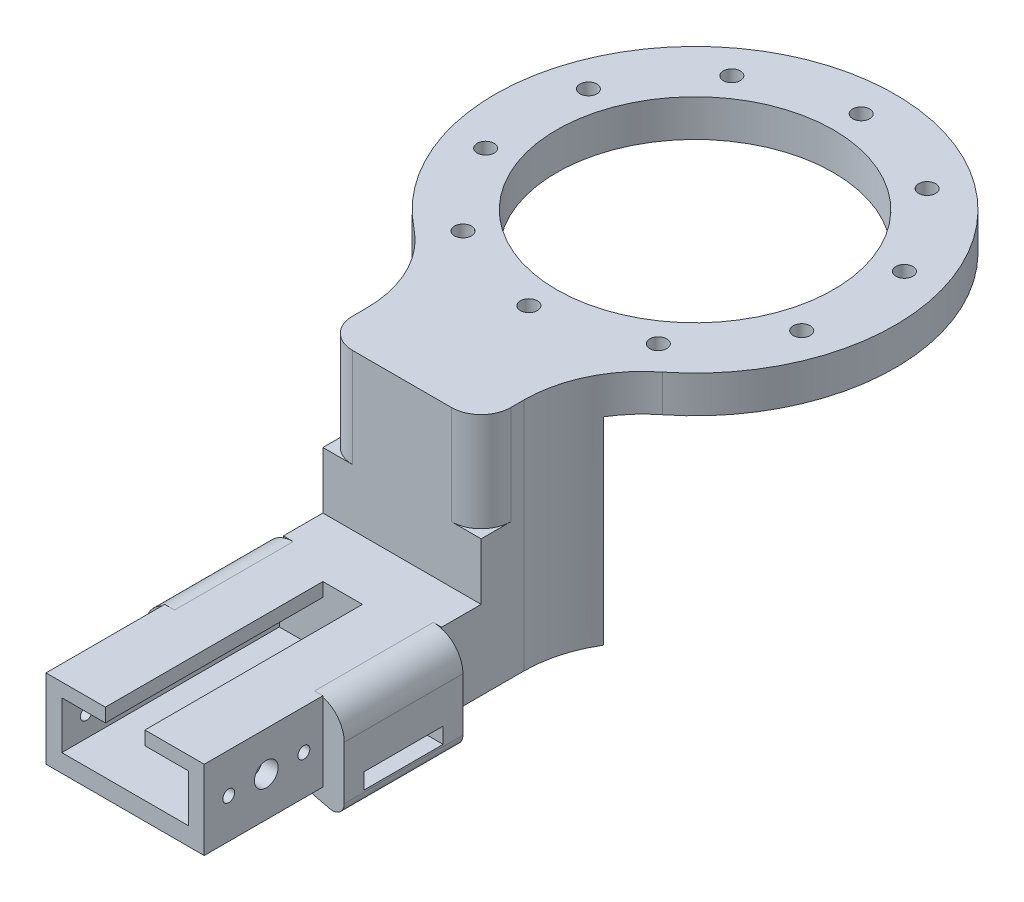
SolidWorks part; units mm, degrees
ref_plane "Front Plane" through (0, 0, 0) normal (0, 0, 1) x (1, 0, 0)
ref_plane "Top Plane" through (0, 0, 0) normal (0, 1, 0) x (1, 0, 0)
ref_plane "Right Plane" through (0, 0, 0) normal (1, 0, 0) x (0, 0, -1)
sketch "Sketch2" plane through (0, 0, 0) normal (0, 1, 0) x (1, 0, 0)
  line L0 (-20, -74.0815) -> (-20, -63.1931)
  line L1 (20, -74.0815) -> (20, -63.1931)
  line L8 (-20, -74.0815) -> (20, -74.0815)
  arc A0 (31.3853, -39.6667) -> (-31.3853, -39.6667) centre (0, 0) ccw
  circle A2 centre (0, 42) radius 2.1524
  circle A3 centre (24.687, 33.9787) radius 2.1524
  circle A4 centre (39.9444, 12.9787) radius 2.1524
  circle A5 centre (39.9444, -12.9787) radius 2.1524
  circle A6 centre (24.687, -33.9787) radius 2.1524
  circle A7 centre (0, -42) radius 2.1524
  circle A8 centre (-24.687, -33.9787) radius 2.1524
  circle A9 centre (-39.9444, -12.9787) radius 2.1524
  circle A10 centre (-39.9444, 12.9787) radius 2.1524
  circle A11 centre (-24.687, 33.9787) radius 2.1524
  circle A12 centre (0, 0) radius 35
  arc A14 (31.3853, -39.6667) -> (20, -63.1931) centre (50, -63.1931) ccw
  arc A15 (-20, -63.1931) -> (-31.3853, -39.6667) centre (-50, -63.1931) ccw
  point P26 (0, 0)
  dimension "D1" = 42
  dimension "D2" = 10
extrude "Boss-Extrude2" add sketch "Sketch2" along normal blind 9.35
sketch "Sketch4" plane through (0, 0, 0) normal (0, -1, 0) x (1, 0, 0)
  line L0 (-20, 74.0815) -> (20, 74.0815)
  line L5 (20, 74.0815) -> (20, 63.1931)
  line L6 (-20, 74.0815) -> (-20, 63.1931)
  arc A0 (20, 63.1931) -> (31.3853, 39.6667) centre (50, 63.1931) ccw construction
  arc A1 (-21.4172, 54.0815) -> (-20, 63.1931) centre (-50, 63.1931) ccw
  arc A2 (-31.3853, 39.6667) -> (-20, 63.1931) centre (-50, 63.1931) ccw construction
  arc A3 (-31.3853, 39.6667) -> (31.3853, 39.6667) centre (0, 0) ccw construction
  arc A4 (20, 63.1931) -> (21.4172, 54.0815) centre (50, 63.1931) ccw
  arc A5 (20, 63.1931) -> (31.3853, 39.6667) centre (50, 63.1931) ccw
  arc A6 (-31.3853, 39.6667) -> (-20, 63.1931) centre (-50, 63.1931) ccw
  circle A9 centre (-2.1524, -48.8892) radius 100
extrude "Boss-Extrude3" add sketch "Sketch4" along normal blind 50
sketch "Sketch6" plane through (0, 9.35, 0) normal (0, 1, 0) x (1, 0, 0)
  line L0 (20, -74.0815) -> (20, -63.1931) construction
  line L1 (-20, -74.0815) -> (20, -74.0815) construction
  line L2 (-20, -63.1931) -> (-20, -74.0815) construction
  line L3 (-12.5, -74.0815) -> (-20, -74.0815)
  line L4 (-20, -74.0815) -> (-20, -66.5815)
  line L5 (12.5, -74.0815) -> (20, -74.0815)
  line L6 (20, -74.0815) -> (20, -66.5815)
  arc A0 (-20, -66.5815) -> (-12.5, -74.0815) centre (-12.5, -66.5815) ccw
  arc A1 (12.5, -74.0815) -> (20, -66.5815) centre (12.5, -66.5815) ccw
extrude "Cut-Extrude2" cut sketch "Sketch6" against normal blind 25
ref_plane "Plane1" through (0, -50, 0) normal (0, -1, 0) x (-1, 0, 0)
sketch "Sketch8" plane through (0, -50, 0) normal (0, -1, 0) x (-1, 0, 0)
  line L0 (-20, -74.0815) -> (20, -74.0815)
  line L1 (20, -74.0815) -> (20, -84.0815)
  line L2 (20, -84.0815) -> (-20, -84.0815)
  line L3 (-20, -84.0815) -> (-20, -74.0815)
extrude "Boss-Extrude4" add sketch "Sketch8" against normal blind 20
ref_plane "Plane3" through (0, 0, 84.0815) normal (0, 0, 1) x (1, 0, 0)
sketch "Sketch10" plane through (0, 0, 84.0815) normal (0, 0, 1) x (1, 0, 0)
  line L2 (-25, -37.5) -> (-25, -50.9515)
  line L3 (25.3946, -37.5) -> (25.3946, -50.9515)
  line L5 (-17.5, -30) -> (17.8946, -30)
  arc A1 (-17.5, -30) -> (-25, -37.5) centre (-17.5, -37.5) ccw
  arc A2 (25.3946, -37.5) -> (17.8946, -30) centre (17.8946, -37.5) ccw
  arc A5 (21.5923, -53.8422) -> (-21.1977, -53.8422) centre (0.1973, -130.9282) ccw
  arc A6 (-25, -50.9515) -> (-21.1977, -53.8422) centre (-22, -50.9515) ccw
  arc A7 (21.5923, -53.8422) -> (25.3946, -50.9515) centre (22.3946, -50.9515) ccw
extrude "Boss-Extrude5" add sketch "Sketch10" along normal blind 30
sketch "Sketch11" plane through (-25, 0, 0) normal (-1, 0, 0) x (0, 0, 1)
  line L0 (99.0815, -50.9515) -> (99.0815, -50.4515)
  line L7 (114.0815, -50.9515) -> (84.0815, -50.9515) construction
  line L8 (99.0815, -50.4515) -> (109.0815, -50.4515)
  line L9 (99.0815, -50.4515) -> (89.0815, -50.4515)
  line L10 (89.0815, -50.4515) -> (89.0815, -46.4515)
  line L11 (89.0815, -46.4515) -> (109.0815, -46.4515)
  line L12 (109.0815, -46.4515) -> (109.0815, -50.4515)
extrude "Cut-Extrude4" cut sketch "Sketch11" against normal blind 56 contours L12 L11 L10 L9 L8
ref_plane "Plane6" through (0, 0, 114.0815) normal (0, 0, 1) x (1, 0, 0)
sketch "Sketch15" plane through (0, 0, 114.0815) normal (0, 0, 1) x (1, 0, 0)
  line L0 (-20, -30) -> (20, -30)
  line L1 (20, -30) -> (20, -50)
  line L2 (-28.6072, -50) -> (28.6072, -50) construction
  line L3 (20, 9.35) -> (20, -50) construction
  line L4 (20, -50) -> (-20, -50)
  line L5 (-20, 9.35) -> (-20, -50) construction
  line L6 (-20, -50) -> (-20, -30)
extrude "Boss-Extrude6" add sketch "Sketch15" along normal blind 30
ref_plane "Plane7" through (-25, -46.4515, 109.0815) normal (0, 0, 1) x (1, 0, 0)
sketch "Sketch16" plane through (-25, -46.4515, 109.0815) normal (0, 0, 1) x (1, 0, 0)
  line L0 (0, 0) -> (0, 1)
  line L1 (0, 1) -> (-2.7816, 1)
ref_plane "Plane8" through (0, 0, 144.0815) normal (0, 0, 1) x (1, 0, 0)
sketch "Sketch17" plane through (0, 0, 144.0815) normal (0, 0, 1) x (1, 0, 0)
  line L0 (-16, -33.4515) -> (-5, -33.4515)
  line L2 (16, -33.4515) -> (5, -33.4515)
  line L3 (-5, -33.4515) -> (-5, -30)
  line L4 (-16, -33.4515) -> (-5, -33.4515)
  line L5 (16, -45.4515) -> (16, -33.4515)
  line L6 (-16, -45.4515) -> (-16, -33.4515)
  line L7 (-16, -45.4515) -> (16, -45.4515)
  line L8 (20, -30) -> (-20, -30) construction
  line L9 (-5, -30) -> (5, -30)
  line L10 (5, -30) -> (5, -33.4515)
  line L11 (5, -33.4515) -> (16, -33.4515)
extrude "Cut-Extrude5" cut sketch "Sketch17" against normal blind 55 contours L10 L9 L3 L0 L6 L7 L5 L2
sketch "Sketch18" plane through (20, 0, 0) normal (1, 0, 0) x (0, 0, -1)
  line L2 (-144.0815, -30) -> (-114.0815, -30) construction
  circle A3 centre (-128.3929, -40) radius 3
  circle A4 centre (-118.8929, -40) radius 1.5
  circle A5 centre (-137.8929, -40) radius 1.5
  dimension "D1" = 10
  dimension "D2" = 9.5
  dimension "D3" = 9.5
extrude "Cut-Extrude6" cut sketch "Sketch18" against normal blind 42
